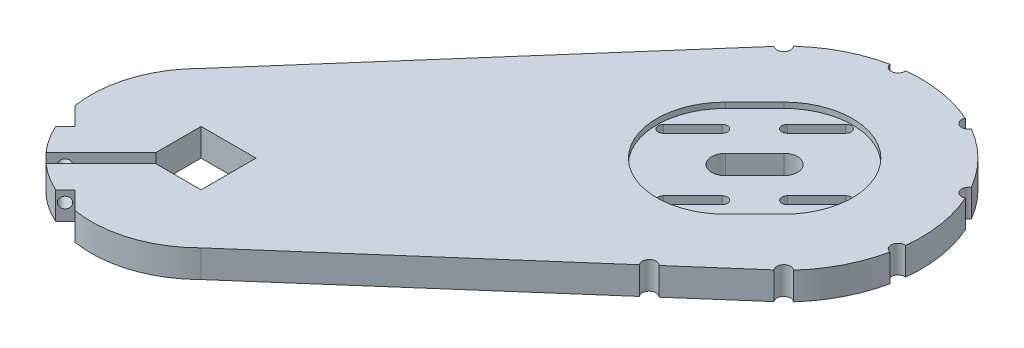
SolidWorks part; units mm, degrees
material "1060-H12"
ref_plane "Plan de face" through (0, 0, 0) normal (0, 0, 1) x (1, 0, 0)
ref_plane "Plan de dessus" through (0, 0, 0) normal (0, 1, 0) x (1, 0, 0)
ref_plane "Plan de droite" through (0, 0, 0) normal (1, 0, 0) x (0, 0, -1)
sketch "Esquisse1" plane through (0, 0, 0) normal (0, 1, 0) x (1, 0, 0)
  line L0 (0, 0) -> (106.066, 106.066) construction
  line L1 (-10, 10) -> (10, 10)
  line L2 (-10, 10) -> (-10, -10)
  line L3 (-10, -10) -> (10, -10)
  line L4 (10, 10) -> (10, -10)
  line L5 (-10, 10) -> (10, -10) construction
  line L6 (-10, -10) -> (10, 10) construction
  line L7 (106.066, 106.066) -> (141.4214, 70.7107) construction
  line L8 (0, 0) -> (28.2843, -28.2843) construction
  line L9 (28.2843, -28.2843) -> (141.4214, 70.7107)
  line L10 (-28.2843, 28.2843) -> (70.7107, 141.4214)
  arc A0 (70.7107, 141.4214) -> (141.4214, 70.7107) centre (106.066, 106.066) cw
  arc A1 (-28.2843, 28.2843) -> (28.2843, -28.2843) centre (0, 0) ccw
  dimension "D3" = 150
  dimension "D1" = 20
  dimension "D4" = 50
  dimension "D2" = 20
  dimension "D5" = 40
extrude "Boss.-Extru.1" add sketch "Esquisse1" along normal blind 10 contours L10 A1 L9 A0 L1 L4 L3 L2
sketch "Esquisse3" plane through (0, 10, 0) normal (0, 1, 0) x (1, 0, 0)
  line L0 (-10, -10) -> (-28.5289, -28.5289) construction
  line L3 (-8.2322, -11.7678) -> (-27.2344, -30.7699)
  line L4 (-27.2344, -30.7699) -> (-30.7699, -27.2344)
  line L5 (-30.7699, -27.2344) -> (-11.7678, -8.2322)
  line L6 (-11.7678, -8.2322) -> (-9.7269, -6.1913)
  line L7 (-9.7269, -6.1913) -> (-6.1913, -9.7269)
  line L8 (-6.1913, -9.7269) -> (-8.2322, -11.7678)
  line L9 (-8.2322, -11.7678) -> (-8.2082, -11.7266)
  point P3 (-19.2631, -19.2631)
  dimension "D1" = 13.1
  dimension "D2" = 2.5
  dimension "D3" = 2.5
extrude "Enlèv. mat.-Extru.1" cut sketch "Esquisse3" against normal through all
ref_plane "Plan1" through (0, 0, 0) normal (0.7071, 0, 0.7071) x (0.7071, 0, -0.7071)
sketch "Esquisse4" plane through (1.7678, 0, 1.7678) normal (-0.7071, 0, -0.7071) x (-0.7071, 0, 0.7071)
  line L0 (11.6421, 10) -> (39.9218, 10) construction
  line L1 (39.9218, 0) -> (39.9218, 10) construction
  circle A0 centre (35.0228, 6) radius 2
  point P0 (35.0228, 6)
  point P5 (39.9218, 5)
  dimension "D1" = 4
  dimension "D2" = 5
extrude "Enlèv. mat.-Extru.2" cut sketch "Esquisse4" against normal through all and the other way through all
sketch "Esquisse5" plane through (0, 10, 0) normal (0, 1, 0) x (1, 0, 0)
  line L0 (-29.9967, -26.4612) -> (-26.4612, -22.9257) construction
  line L1 (-29.9967, -26.4612) -> (-10, -6.4645) construction
  line L2 (-26.4612, -22.9257) -> (-41.741, -7.6459) construction
  line L3 (-34.6837, -14.7032) -> (-36.4514, -16.471)
  line L4 (-36.4514, -16.471) -> (-40.9085, -7.7776)
  line L5 (-40.9085, -7.7776) -> (-39.4911, -6.3602)
  line L6 (-39.4911, -6.3602) -> (-32.9159, -12.9355)
  line L7 (-32.9159, -12.9355) -> (-34.6837, -14.7032)
  line L8 (-28.8576, -28.8576) -> (-15.8397, -15.8397) construction
  line L9 (-3.1113, -3.1113) -> (3.1113, 3.1113) construction
  line L10 (-7.7776, -40.9085) -> (-6.3602, -39.4911)
  line L11 (-16.471, -36.4514) -> (-7.7776, -40.9085)
  line L12 (-14.7032, -34.6837) -> (-16.471, -36.4514)
  line L13 (-12.9355, -32.9159) -> (-14.7032, -34.6837)
  line L14 (-6.3602, -39.4911) -> (-12.9355, -32.9159)
  arc A0 (-28.2843, 28.2843) -> (-29.9967, -26.4612) centre (0, 0) ccw construction
  dimension "D1" = 5
  dimension "D2" = 2.5
  dimension "D3" = 2.5
extrude "Enlèv. mat.-Extru.3" cut sketch "Esquisse5" against normal through all
sketch "Esquisse7" plane through (0, 10, 0) normal (0, 1, 0) x (1, 0, 0)
  line L0 (0, 0) -> (106.066, 106.066) construction
  line L1 (106.066, 106.066) -> (141.4214, 70.7107) construction
  line L2 (10, 10) -> (106.066, 106.066) construction
  line L6 (106.066, 106.066) -> (109.6016, 109.6016) construction
  line L7 (95.4594, 95.4594) -> (66.5612, 95.4594) construction
  line L8 (95.4594, 95.4594) -> (106.066, 106.066) construction
  line L9 (91.9239, 98.9949) -> (102.5305, 109.6016)
  line L10 (98.9949, 91.9239) -> (109.6016, 102.5305)
  line L11 (106.066, 106.066) -> (106.066, 143.8436) construction
  line L12 (95.4594, 95.4594) -> (95.4594, 136.3981) construction
  line L13 (106.066, 106.066) -> (72.9746, 106.066) construction
  line L26 (95.4594, 117.9594) -> (106.066, 128.566) construction
  line L27 (94.0452, 119.3736) -> (104.6518, 129.9802)
  line L28 (96.8736, 116.5452) -> (107.4802, 127.1518)
  line L29 (72.9594, 95.4594) -> (83.566, 106.066) construction
  line L30 (71.5452, 96.8736) -> (82.1518, 107.4802)
  line L31 (74.3736, 94.0452) -> (84.9802, 104.6518)
  line L32 (117.9594, 95.4594) -> (128.566, 106.066) construction
  line L33 (119.3736, 94.0452) -> (129.9802, 104.6518)
  line L34 (116.5452, 96.8736) -> (127.1518, 107.4802)
  line L35 (95.4594, 72.9594) -> (106.066, 83.566) construction
  line L36 (96.8736, 71.5452) -> (107.4802, 82.1518)
  line L37 (94.0452, 74.3736) -> (104.6518, 84.9802)
  arc A0 (91.9239, 98.9949) -> (98.9949, 91.9239) centre (95.4594, 95.4594) ccw
  arc A1 (109.6016, 102.5305) -> (102.5305, 109.6016) centre (106.066, 106.066) ccw
  arc A10 (94.0452, 119.3736) -> (96.8736, 116.5452) centre (95.4594, 117.9594) ccw
  arc A11 (107.4802, 127.1518) -> (104.6518, 129.9802) centre (106.066, 128.566) ccw
  arc A12 (71.5452, 96.8736) -> (74.3736, 94.0452) centre (72.9594, 95.4594) ccw
  arc A13 (84.9802, 104.6518) -> (82.1518, 107.4802) centre (83.566, 106.066) ccw
  arc A14 (119.3736, 94.0452) -> (116.5452, 96.8736) centre (117.9594, 95.4594) cw
  arc A15 (127.1518, 107.4802) -> (129.9802, 104.6518) centre (128.566, 106.066) cw
  arc A16 (96.8736, 71.5452) -> (94.0452, 74.3736) centre (95.4594, 72.9594) cw
  arc A17 (104.6518, 84.9802) -> (107.4802, 82.1518) centre (106.066, 83.566) cw
  point P0 (106.066, 106.066)
  point P8 (95.4594, 95.4594)
  point P13 (100.7627, 100.7627)
  point P21 (106.066, 121.066)
  point P24 (95.4594, 110.4594)
  point P25 (91.066, 106.066)
  point P26 (80.4594, 95.4594)
  point P55 (106.066, 128.566)
  point P56 (95.4594, 117.9594)
  point P57 (83.566, 106.066)
  point P58 (72.9594, 95.4594)
  point P59 (100.7627, 123.2627)
  point P68 (78.2627, 100.7627)
  point P75 (123.2627, 100.7627)
  point P82 (100.7627, 78.2627)
  dimension "D4" = 45
  dimension "D11" = 15
  dimension "D1" = 5
  dimension "D2" = 15
  dimension "D3" = 45
  dimension "D5" = 45
  dimension "D6" = 45
  dimension "D7" = 15
  dimension "D8" = 15
  dimension "D9" = 15
  dimension "D10" = 15
  dimension "D12" = 22.5
  dimension "D13" = 22.5
  dimension "D14" = 22.5
  dimension "D15" = 22.5
extrude "Enlèv. mat.-Extru.4" cut sketch "Esquisse7" against normal through all
sketch "Esquisse8" plane through (0, 10, 0) normal (0, 1, 0) x (1, 0, 0)
  line L0 (106.066, 106.066) -> (95.4594, 95.4594) construction
  line L1 (123.7437, 88.3883) -> (113.1371, 77.7817)
  line L2 (88.3883, 123.7437) -> (77.7817, 113.1371)
  arc A0 (123.7437, 88.3883) -> (88.3883, 123.7437) centre (106.066, 106.066) ccw
  arc A1 (77.7817, 113.1371) -> (113.1371, 77.7817) centre (95.4594, 95.4594) ccw
  point P2 (106.066, 106.066)
  point P3 (95.4594, 95.4594)
  point P5 (100.7627, 100.7627)
extrude "Enlèv. mat.-Extru.5" cut sketch "Esquisse8" against normal blind 2
ref_plane "Plan2" through (0, 5, 0) normal (0, 1, 0) x (1, 0, 0)
sketch "Esquisse9" plane through (0, 0, 0) normal (0, -1, 0) x (-1, 0, 0)
  line L0 (-70.7107, 141.4214) -> (-106.066, 106.066) construction
  line L1 (0, 0) -> (-106.066, 106.066) construction
  line L2 (-155.4504, 98.2443) -> (-106.066, 106.066) construction
  line L4 (-106.066, 106.066) -> (-115.2875, 47.8436) construction
  line L5 (-106.066, 106.066) -> (-141.4214, 70.7107) construction
  line L6 (-28.2843, -28.2843) -> (-141.4214, 70.7107) construction
  circle A0 centre (-70.7107, 141.4214) radius 2.5
  circle A1 centre (-98.2443, 155.4504) radius 2.5
  circle A2 centre (-128.7655, 150.6163) radius 2.5
  circle A3 centre (-150.6163, 128.7655) radius 2.5
  circle A4 centre (-155.4504, 98.2443) radius 2.5
  circle A5 centre (-141.4214, 70.7107) radius 2.5
  circle A6 centre (-115.2875, 47.8436) radius 2.5
  point P19 (-106.066, 106.066)
  dimension "D2" = 6
  dimension "D3" = 36
  dimension "D1" = 50
extrude "Enlèv. mat.-Extru.6" cut sketch "Esquisse9" against normal through all
